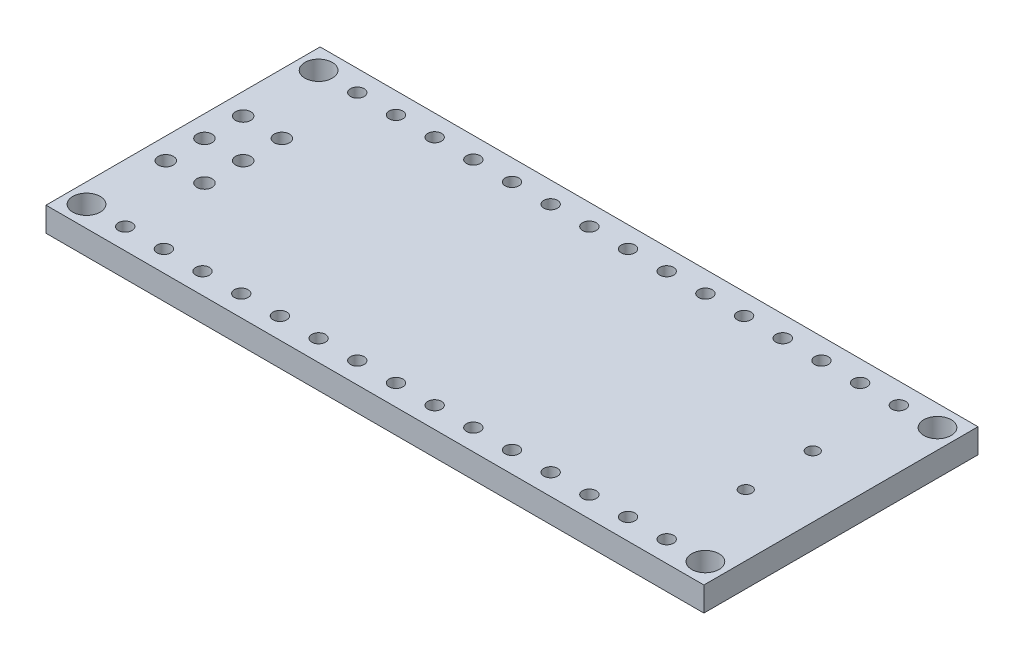
SolidWorks part; units mm, degrees
material "E-Glass Fiber"
ref_plane "Front Plane" through (0, 0, 0) normal (0, 0, 1) x (1, 0, 0)
ref_plane "Top Plane" through (0, 0, 0) normal (0, 1, 0) x (1, 0, 0)
ref_plane "Right Plane" through (0, 0, 0) normal (1, 0, 0) x (0, 0, -1)
sketch "Sketch1" plane through (0, 0, 0) normal (0, 1, 0) x (1, 0, 0)
  line L0 (0, 7.62) -> (-3.82, 7.62) construction
  line L1 (-3.82, 16.62) -> (39.38, 16.62)
  line L2 (-3.82, 16.62) -> (-3.82, -1.38)
  line L3 (-3.82, -1.38) -> (39.38, -1.38)
  line L4 (39.38, 16.62) -> (39.38, -1.38)
  line L5 (0, 0) -> (35.56, 0) construction
  line L6 (0, 0) -> (0, 15.24) construction
  line L7 (0, 15.24) -> (35.56, 15.24) construction
  line L8 (35.56, 0) -> (35.56, 15.24) construction
  line L10 (35.56, 7.62) -> (39.38, 7.62) construction
  dimension "D1" = 43.2
  dimension "D2" = 18
  dimension "D3" = 15.24
  dimension "D4" = 35.56
extrude "Boss-Extrude2" add sketch "Sketch1" along normal blind 1.6
sketch "Sketch2" plane through (0, 0, 0) normal (0, 1, 0) x (1, 0, 0)
  line L0 (0, -0.88) -> (0, 0.88) construction
  line L2 (-0.88, 0) -> (0.88, 0) construction
  circle A0 centre (0, 0) radius 0.45
  circle A1 centre (0, 15.24) radius 0.45
  dimension "D1" = 0.9
  dimension "D2" = 15.24
extrude "Cut-Extrude2" cut sketch "Sketch2" along normal blind 1.6
pattern_linear "LPattern1" count 15 spacing 2.54 along (1, 0, 0) of "Cut-Extrude2"
sketch "Sketch3" plane through (0, 0, 0) normal (0, 1, 0) x (1, 0, 0)
  line L1 (-0.88, 0) -> (0.88, 0) construction
  line L2 (0, -0.88) -> (0, 0.88) construction
  circle A0 centre (0.127, 10.16) radius 0.5
  circle A1 centre (-2.413, 10.16) radius 0.5
  circle A2 centre (-2.413, 7.62) radius 0.5
  circle A3 centre (-2.413, 5.08) radius 0.5
  circle A4 centre (0.127, 5.08) radius 0.5
  circle A5 centre (0.127, 7.62) radius 0.5
  dimension "D1" = 1
  dimension "D5" = 7.62
  dimension "D2" = 2.54
  dimension "D3" = 2.54
  dimension "D4" = 2.54
  dimension "D6" = 2.54
  dimension "D7" = 0.127
extrude "Cut-Extrude4" cut sketch "Sketch3" along normal blind 1.6
sketch "Sketch4" plane through (0, 0, 0) normal (0, 1, 0) x (1, 0, 0)
  line L0 (-0.88, 0) -> (0.88, 0) construction
  line L1 (0, -0.88) -> (0, 0.88) construction
  circle A0 centre (38.1, 15.24) radius 0.9
  circle A1 centre (38.1, 0) radius 0.9
  circle A2 centre (-2.54, 0) radius 0.9
  circle A3 centre (-2.54, 15.24) radius 0.9
  dimension "D3" = 1.8
  dimension "D1" = 40.64
  dimension "D2" = 2.54
  dimension "D4" = 15.24
  dimension "D5" = 15.24
extrude "Cut-Extrude5" cut sketch "Sketch4" along normal blind 1.6
sketch "Sketch5" plane through (0, 1.6, 0) normal (0, 1, 0) x (1, 0, 0)
  circle A0 centre (38.1, 15.24) radius 0.9
  circle A1 centre (38.1, 15.24) radius 1.275
  circle A2 centre (38.1, 15.24) radius 0.9 construction
  circle A3 centre (38.1, 0) radius 0.9
  circle A4 centre (38.1, 0) radius 0.9 construction
  circle A5 centre (38.1, 0) radius 1.275
  circle A6 centre (-2.54, 15.24) radius 0.9
  circle A7 centre (-2.54, 15.24) radius 1.275
  circle A8 centre (-2.54, 0) radius 0.9
  circle A9 centre (-2.54, 0) radius 1.275
  circle A10 centre (-2.54, 15.24) radius 0.9 construction
  circle A11 centre (-2.54, 0) radius 0.9 construction
  dimension "D1" = 2.55
extrude "Boss-Extrude3" [suppressed] add sketch "Sketch5" along normal blind 0.1
sketch "Sketch6" plane through (0, 0, 0) normal (1, 0, 0) x (0, 0, -1)
  line L0 (0, 1.6) -> (0.9, 1.6)
  line L1 (-1.38, 1.6) -> (16.62, 1.6) construction
  line L2 (0.2252, 3.1) -> (0, 3.1)
  line L3 (0, 2.53) -> (0, -2.53) construction
  line L4 (0, 3.1) -> (0, 1.6)
  line L5 (0, 1.3722) -> (0, 3.4408) construction
  arc A0 (0.9, 1.6) -> (0.7139, 2.2122) centre (-0.2, 1.6) ccw
  arc A1 (0.7139, 2.2122) -> (0.4221, 2.9352) centre (2.2924, 3.2697) cw
  arc A2 (0.4221, 2.9352) -> (0.2252, 3.1) centre (0.2252, 2.9) ccw
  point P16 (0.4, 3.1)
  dimension "D4" = 1.1
  dimension "D5" = 1.9
  dimension "D6" = 0.2
  dimension "D1" = 1.5
  dimension "D2" = 0.8
  dimension "D3" = 1.8
revolve "Revolve1" [suppressed] add sketch "Sketch6" angle 360 about L5
pattern_linear "LPattern2" [suppressed] count 2 spacing 15.24 count 15 spacing 2.54
ref_plane "Plane3" through (0, 0, -5.08) normal (0, 0, 1) x (1, 0, 0)
sketch "Sketch7" plane through (0, 0, -5.08) normal (0, 0, 1) x (1, 0, 0)
  line L0 (0.127, 3.889) -> (0.127, -2.5597) construction
  line L2 (0, -1.705) -> (0, 1.705) construction
  line L3 (0.127, 0) -> (1.027, 0)
  line L4 (9.9, 0) -> (-9.9, 0) construction
  line L5 (0.127, 0) -> (0.127, -1.5)
  line L6 (0.127, -1.5) -> (0.3395, -1.5)
  arc A0 (0.538, -1.325) -> (0.807, -0.66) centre (1.927, -1.5) cw
  arc A1 (0.807, -0.66) -> (1.027, 0) centre (-0.073, 0) ccw
  arc A2 (0.3395, -1.5) -> (0.538, -1.325) centre (0.3395, -1.3) ccw
  point P16 (0.527, -1.5)
  dimension "D5" = 1.1
  dimension "D6" = 0.2
  dimension "D1" = 0.127
  dimension "D2" = 1.5
  dimension "D3" = 0.8
  dimension "D4" = 1.8
revolve "Revolve2" [suppressed] add sketch "Sketch7" angle 360 about L0
pattern_linear "LPattern3" [suppressed] count 2 spacing 2.54 count 3 spacing 2.54
sketch "Sketch8" plane through (0, 0, 0) normal (0, -1, 0) x (1, 0, 0)
  circle A0 centre (38.1, 0) radius 0.9
  circle A1 centre (38.1, 0) radius 1.275
  circle A2 centre (38.1, -15.24) radius 1.275
  circle A3 centre (38.1, -15.24) radius 0.9
  circle A4 centre (38.1, -15.24) radius 0.9 construction
  circle A5 centre (38.1, 0) radius 0.9 construction
  circle A6 centre (-2.54, 0) radius 0.9
  circle A7 centre (-2.54, 0) radius 1.275
  circle A8 centre (-2.54, -15.24) radius 0.9
  circle A9 centre (-2.54, -15.24) radius 1.275
  circle A10 centre (-2.54, 0) radius 0.9 construction
  circle A11 centre (-2.54, -15.24) radius 0.9 construction
  dimension "D1" = 2.55
extrude "Boss-Extrude4" [suppressed] add sketch "Sketch8" along normal blind 0.1
sketch "Sketch9" plane through (0, 0, 0) normal (0, 1, 0) x (1, 0, 0)
  line L0 (-1.705, 0) -> (1.705, 0) construction
  line L1 (39.38, -1.38) -> (39.38, 16.62) construction
  circle A0 centre (35.33, 5.42) radius 0.4
  circle A1 centre (35.33, 9.82) radius 0.4
  dimension "D1" = 0.8
  dimension "D2" = 4.4
  dimension "D3" = 5.42
  dimension "D4" = 4.05
extrude "Cut-Extrude6" cut sketch "Sketch9" along normal blind 10
